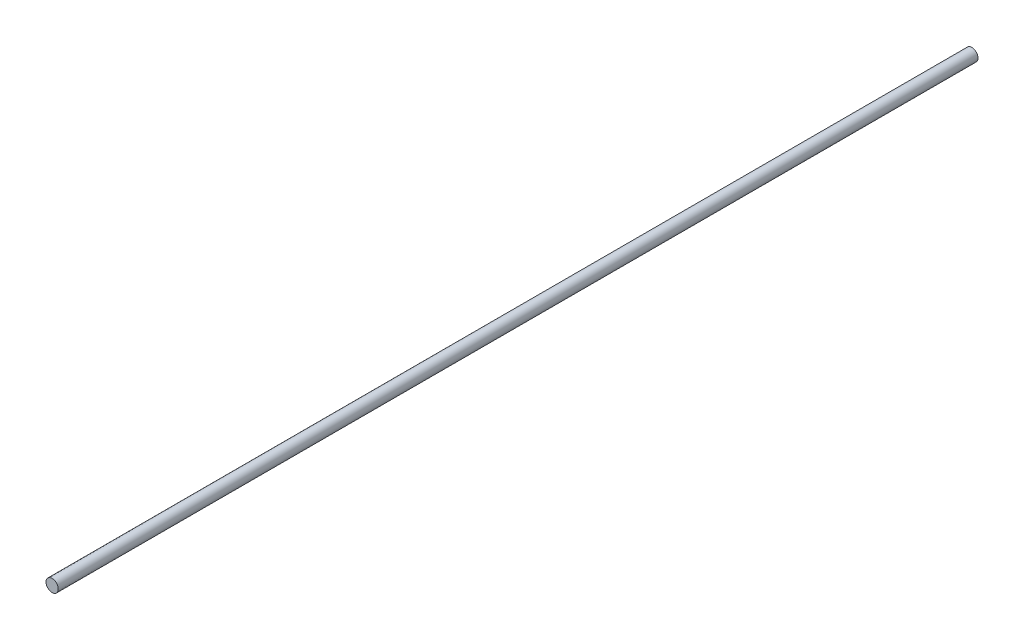
SolidWorks part; units mm, degrees
material "AISI 304"
ref_plane "Front Plane" through (0, 0, 0) normal (0, 0, 1) x (1, 0, 0)
ref_plane "Top Plane" through (0, 0, 0) normal (0, 1, 0) x (1, 0, 0)
ref_plane "Right Plane" through (0, 0, 0) normal (1, 0, 0) x (0, 0, -1)
sketch "Sketch1" plane through (0, 0, 0) normal (0, 0, 1) x (1, 0, 0)
  circle A0 centre (0, 0) radius 4
  dimension "D1" = 8
extrude "Boss-Extrude1" add sketch "Sketch1" along normal blind 600
sketch "Sketch2" plane through (0, 0, 600) normal (0, 0, 1) x (1, 0, 0)
  line L0 (0, 4) -> (0, -4)
  line L1 (-4, 0) -> (4, 0)
  circle A0 centre (0, 0) radius 4 construction
